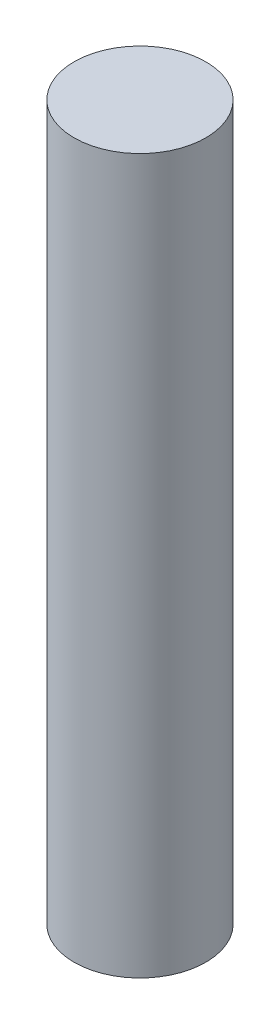
SolidWorks part; units mm, degrees
ref_plane "Front Plane" through (0, 0, 0) normal (0, 0, 1) x (1, 0, 0)
ref_plane "Top Plane" through (0, 0, 0) normal (0, 1, 0) x (1, 0, 0)
ref_plane "Right Plane" through (0, 0, 0) normal (1, 0, 0) x (0, 0, -1)
sketch "Sketch1" plane through (0, 0, 0) normal (0, 1, 0) x (1, 0, 0)
  line L0 (0, 0) -> (-109.2351, -37.0849) construction
  circle A0 centre (0, 45.445) radius 1.925
extrude "Boss-Extrude1" add sketch "Sketch1" along normal blind 20.86
